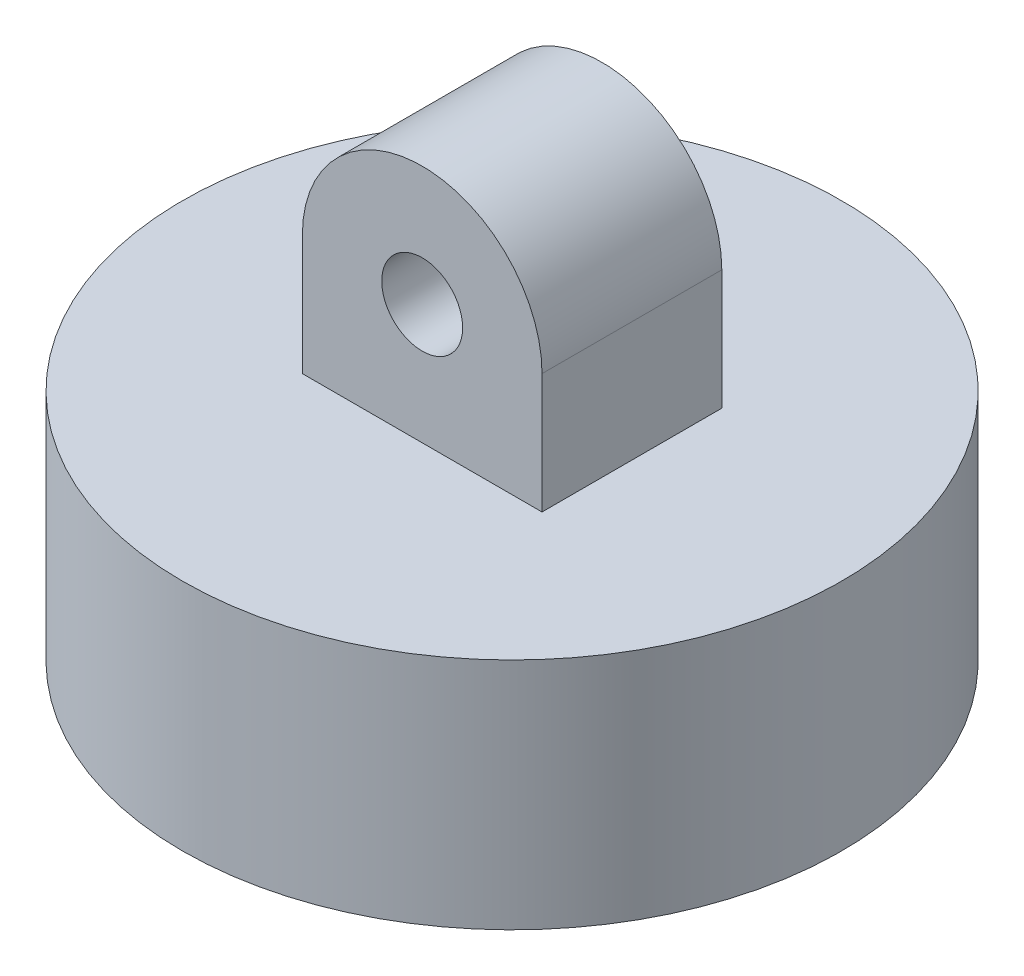
SolidWorks part; units mm, degrees
ref_plane "Front Plane" through (0, 0, 0) normal (0, 0, 1) x (1, 0, 0)
ref_plane "Top Plane" through (0, 0, 0) normal (0, 1, 0) x (1, 0, 0)
ref_plane "Right Plane" through (0, 0, 0) normal (1, 0, 0) x (0, 0, -1)
sketch "Sketch1" plane through (0, 0, 0) normal (0, 1, 0) x (1, 0, 0)
  circle A0 centre (0, 0) radius 13.97
  circle A1 centre (0, 0) radius 8.89
  dimension "D1" = 17.78
  dimension "D2" = 27.94
extrude "Boss-Extrude1" add sketch "Sketch1" along normal blind 4.826
sketch "Sketch2" plane through (0, 4.826, 0) normal (0, 1, 0) x (1, 0, 0)
  circle A0 centre (0, 0) radius 13.97
extrude "Boss-Extrude2" add sketch "Sketch2" along normal blind 5.08
sketch "Sketch3" plane through (0, 0, 0) normal (0, 0, 1) x (1, 0, 0)
  line L0 (-5.08, 9.906) -> (-5.08, 14.986)
  line L1 (13.97, 9.906) -> (-13.97, 9.906) construction
  line L2 (5.08, 14.986) -> (5.08, 9.906)
  line L3 (5.08, 9.906) -> (-5.08, 9.906)
  arc A0 (-5.08, 14.986) -> (5.08, 14.986) centre (0, 14.986) cw
  circle A1 centre (0, 14.986) radius 1.7145
  dimension "D1" = 5.08
  dimension "D3" = 3.429
  dimension "D2" = 5.08
extrude "Boss-Extrude3" add sketch "Sketch3" along normal mid plane 7.62
